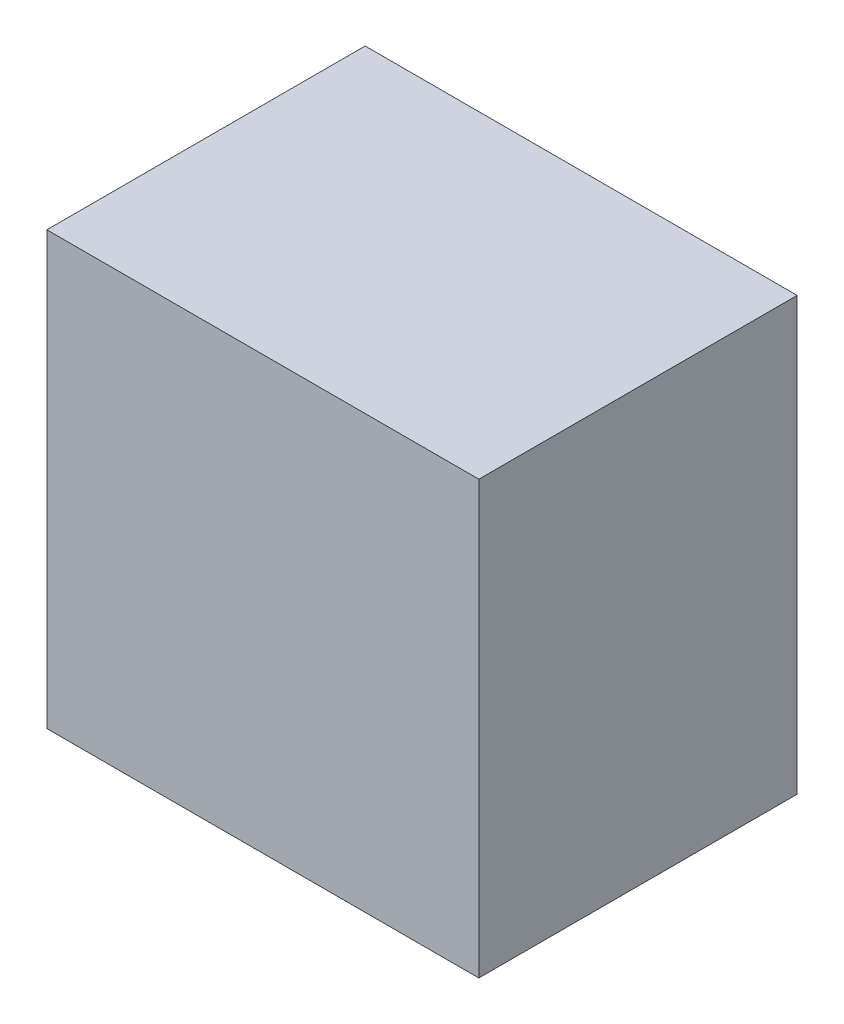
SolidWorks part; units mm, degrees
ref_plane "Plan de face" through (0, 0, 0) normal (0, 0, 1) x (1, 0, 0)
ref_plane "Plan de dessus" through (0, 0, 0) normal (0, 1, 0) x (1, 0, 0)
ref_plane "Plan de droite" through (0, 0, 0) normal (1, 0, 0) x (0, 0, -1)
sketch "Esquisse1" plane through (0, 0, 0) normal (0, 0, 1) x (1, 0, 0)
  line L1 (-170, 170) -> (170, 170)
  line L2 (-170, 170) -> (-170, -170)
  line L3 (-170, -170) -> (170, -170)
  line L4 (170, 170) -> (170, -170)
  line L5 (-170, 170) -> (170, -170) construction
  line L6 (-170, -170) -> (170, 170) construction
  line L7 (-190, 190) -> (190, 190)
  line L8 (-190, 190) -> (-190, -190)
  line L9 (-190, -190) -> (190, -190)
  line L10 (190, 190) -> (190, -190)
  line L11 (-190, 190) -> (190, -190) construction
  line L12 (-190, -190) -> (190, 190) construction
  point P0 (0, 0)
  point P6 (0, 0)
  dimension "D1" = 340
  dimension "D2" = 340
  dimension "D3" = 380
  dimension "D4" = 380
extrude "Boss.-Extru.1" add sketch "Esquisse1" along normal blind 260
sketch "Esquisse2" plane through (0, 0, 260) normal (0, 0, 1) x (1, 0, 0)
  line L1 (-190, 190) -> (190, 190)
  line L2 (-190, 190) -> (-190, -190)
  line L3 (-190, -190) -> (190, -190)
  line L4 (190, 190) -> (190, -190)
  line L5 (-190, 190) -> (190, -190) construction
  line L6 (-190, -190) -> (190, 190) construction
  point P0 (0, 0)
extrude "Boss.-Extru.2" add sketch "Esquisse2" along normal blind 20
